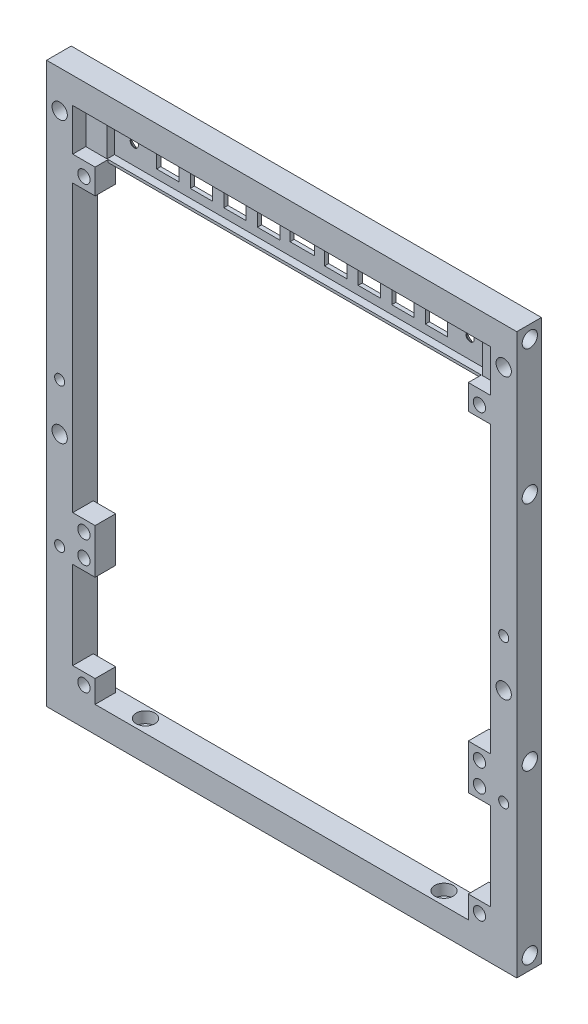
SolidWorks part; units mm, degrees
ref_plane "Front Plane" through (0, 0, 0) normal (0, 0, 1) x (1, 0, 0)
ref_plane "Top Plane" through (0, 0, 0) normal (0, 1, 0) x (1, 0, 0)
ref_plane "Right Plane" through (0, 0, 0) normal (1, 0, 0) x (0, 0, -1)
sketch "Sketch1" plane through (0, 0, 0) normal (0, 0, 1) x (1, 0, 0)
  line L1 (-63, -75) -> (63, -75)
  line L2 (-63, -75) -> (-63, 75)
  line L3 (-63, 75) -> (63, 75)
  line L4 (63, -75) -> (63, 75)
  line L5 (-63, -75) -> (63, 75) construction
  line L6 (-63, 75) -> (63, -75) construction
  line L7 (-56, -68) -> (56, -68)
  line L8 (-56, -68) -> (-56, 68)
  line L9 (-56, 68) -> (56, 68)
  line L10 (56, -68) -> (56, 68)
  line L11 (-56, -68) -> (56, 68) construction
  line L12 (-56, 68) -> (56, -68) construction
  point P0 (0, 0)
  point P6 (0, 0)
  dimension "D1" = 126
  dimension "D2" = 150
  dimension "D3" = 7
  dimension "D4" = 7
extrude "Boss-Extrude1" add sketch "Sketch1" along normal blind 7
sketch "Sketch2" plane through (-63, 0, 0) normal (-1, 0, 0) x (0, 0, 1)
  line L0 (3.5, 71.5) -> (3.5, -71.5) construction
  line L1 (7, 75) -> (0, 75) construction
  circle A0 centre (3.5, -71.5) radius 2.05
  circle A2 centre (3.5, 71.5) radius 2.05
  circle A3 centre (3.5, 35.5) radius 2.05
  circle A4 centre (3.5, -26.5) radius 2.05
  point P2 (3.5, 0)
  point P7 (3.5, 75)
  dimension "D2" = 4.1
  dimension "D3" = 36
  dimension "D4" = 45
  dimension "D1" = 3.5
extrude "Cut-Extrude1" cut sketch "Sketch2" against normal blind 6
mirror "Mirror1" about plane through (0, 0, 0) normal (1, 0, 0) of "Cut-Extrude1"
sketch "Sketch3" plane through (0, -68, 0) normal (0, 1, 0) x (1, 0, 0)
  line L0 (0, 0) -> (0, -7) construction
  line L1 (-56, 0) -> (56, 0) construction
  line L2 (-56, -7) -> (56, -7) construction
  line L3 (40, -3.5) -> (-40, -3.5) construction
  circle A0 centre (40, -3.5) radius 1.35
  circle A1 centre (-40, -3.5) radius 1.35
  point P9 (0, -3.5)
  dimension "D1" = 2.7
  dimension "D2" = 80
extrude "Cut-Extrude2" cut sketch "Sketch3" against normal through all
sketch "Sketch4" plane through (0, -68, 0) normal (0, 1, 0) x (1, 0, 0)
  circle A0 centre (40, -3.5) radius 2.5
  circle A1 centre (-40, -3.5) radius 2.5
  dimension "D1" = 5
extrude "Cut-Extrude3" cut sketch "Sketch4" against normal blind 3
sketch "Sketch5" plane through (0, 0, 0) normal (0, 0, -1) x (-1, 0, 0)
  line L0 (-59.5, -75) -> (-59.5, 75) construction
  line L1 (63, -75) -> (-63, -75) construction
  line L2 (-63, 75) -> (63, 75) construction
  line L3 (-56, 0) -> (-63, 0) construction
  line L4 (-56, -68) -> (-56, 68) construction
  line L5 (-63, -75) -> (-63, 75) construction
  line L6 (0, 75) -> (0, -75) construction
  line L7 (56, -68) -> (-56, -68) construction
  circle A0 centre (-59.5, 2.6) radius 1.35
  circle A1 centre (59.5, 2.6) radius 1.35
  circle A2 centre (-59.5, -36) radius 1.35
  circle A3 centre (59.5, -36) radius 1.35
  point P12 (-59.5, 0)
  point P13 (-59.5, 0)
  dimension "D1" = 2.7
  dimension "D2" = 2.6
  dimension "D3" = 32
extrude "Cut-Extrude4" cut sketch "Sketch5" against normal through all
sketch "Sketch6" plane through (0, 0, 0) normal (0, 0, -1) x (-1, 0, 0)
  circle A0 centre (-59.5, 2.6) radius 2.5
  circle A1 centre (59.5, 2.6) radius 2.5
  circle A2 centre (-59.5, -36) radius 2.5
  circle A3 centre (59.5, -36) radius 2.5
  dimension "D1" = 5
extrude "Cut-Extrude5" cut sketch "Sketch6" against normal blind 3
sketch "Sketch7" plane through (0, 0, 0) normal (0, 0, -1) x (-1, 0, 0)
  line L0 (-56, 68) -> (-63, 68) construction
  line L1 (-63, -75) -> (-63, 75) construction
  line L2 (-59.5, 65) -> (-59.5, -10) construction
  line L3 (-63, 75) -> (63, 75) construction
  circle A0 centre (-59.5, 65) radius 2.05
  circle A1 centre (-59.5, -10) radius 2.05
  point P8 (-59.5, 68)
  dimension "D1" = 4.1
  dimension "D2" = 10
  dimension "D3" = 75
extrude "Cut-Extrude6" cut sketch "Sketch7" against normal through all
mirror "Mirror2" about plane through (0, 0, 0) normal (1, 0, 0) of "Cut-Extrude6"
sketch "Sketch8" plane through (0, 0, 3) normal (0, 0, -1) x (-1, 0, 0)
  line L2 (-60.85, 0.4958) -> (-60.85, 4.7042)
  line L4 (-58.15, 0.4958) -> (-58.15, 4.7042)
  line L5 (-60.85, 0.4958) -> (-58.15, 4.7042) construction
  line L6 (-60.85, 4.7042) -> (-58.15, 0.4958) construction
  line L8 (-60.85, -38.1042) -> (-60.85, -33.8958)
  line L10 (-58.15, -38.1042) -> (-58.15, -33.8958)
  line L11 (-60.85, -38.1042) -> (-58.15, -33.8958) construction
  line L12 (-60.85, -33.8958) -> (-58.15, -38.1042) construction
  circle A0 centre (-59.5, 2.6) radius 2.5 construction
  circle A1 centre (-59.5, -36) radius 2.5 construction
  circle A2 centre (-59.5, -36) radius 2.5 construction
  arc A3 (-58.15, 4.7042) -> (-60.85, 4.7042) centre (-59.5, 2.6) ccw
  arc A4 (-58.15, -33.8958) -> (-60.85, -33.8958) centre (-59.5, -36) ccw
  circle A5 centre (-59.5, 2.6) radius 1.35 construction
  circle A6 centre (-59.5, -36) radius 1.35 construction
  arc A7 (-60.85, -38.1042) -> (-58.15, -38.1042) centre (-59.5, -36) ccw
  arc A8 (-60.85, 0.4958) -> (-58.15, 0.4958) centre (-59.5, 2.6) ccw
  point P0 (-59.5, 2.6)
  point P8 (-59.5, -36)
extrude "Cut-Extrude7" cut sketch "Sketch8" against normal blind 0.2
sketch "Sketch9" plane through (0, 0, 3.2) normal (0, 0, -1) x (-1, 0, 0)
  line L0 (-58.15, 2.6) -> (-58.15, 4.7042) construction
  line L1 (-60.85, 1.25) -> (-58.15, 1.25)
  line L2 (-60.85, 1.25) -> (-60.85, 3.95)
  line L3 (-60.85, 3.95) -> (-58.15, 3.95)
  line L4 (-58.15, 1.25) -> (-58.15, 3.95)
  line L5 (-60.85, 1.25) -> (-58.15, 3.95) construction
  line L6 (-60.85, 3.95) -> (-58.15, 1.25) construction
  line L7 (-58.15, -38.1042) -> (-58.15, -33.8958) construction
  line L8 (-60.85, -37.35) -> (-58.15, -37.35)
  line L9 (-60.85, -37.35) -> (-60.85, -34.65)
  line L10 (-60.85, -34.65) -> (-58.15, -34.65)
  line L11 (-58.15, -37.35) -> (-58.15, -34.65)
  line L12 (-60.85, -37.35) -> (-58.15, -34.65) construction
  line L13 (-60.85, -34.65) -> (-58.15, -37.35) construction
  arc A0 (-58.15, 2.6) -> (-60.85, 2.6) centre (-59.5, 2.6) ccw construction
  point P0 (-59.5, 2.6)
  point P8 (-59.5, -36)
extrude "Cut-Extrude8" cut sketch "Sketch9" against normal blind 0.2
mirror "Mirror3" about plane through (0, 0, 0) normal (1, 0, 0) of "Cut-Extrude8", "Cut-Extrude7"
sketch "Sketch10" plane through (0, 0, 7) normal (0, 0, 1) x (1, 0, 0)
  line L0 (56, -68) -> (56, 68) construction
  line L1 (56, -68) -> (50, -68)
  line L2 (56, -68) -> (56, -62)
  line L3 (56, -62) -> (50, -62)
  line L4 (50, -68) -> (50, -62)
  line L5 (56, -38.5) -> (50, -38.5)
  line L6 (56, -38.5) -> (56, -32.5)
  line L7 (56, -32.5) -> (50, -32.5)
  line L8 (50, -38.5) -> (50, -32.5)
  line L9 (-56, -68) -> (56, -68) construction
  dimension "D1" = 6
  dimension "D2" = 35.5
extrude "Boss-Extrude2" add sketch "Sketch10" against normal offset from surface (5.5 mm away) 1.5 up to face at (-57.45, -10, 0)
sketch "Sketch11" plane through (0, 0, 1.5) normal (0, 0, -1) x (-1, 0, 0)
  line L0 (-56, -38.5) -> (-50, -32.5) construction
  line L2 (-56, -68) -> (-50, -62) construction
  circle A0 centre (-53, -35.5) radius 1.65
  circle A1 centre (-53, -65) radius 1.65
  dimension "D1" = 3.3
extrude "Cut-Extrude9" cut sketch "Sketch11" against normal through all
mirror "Mirror4" about plane through (0, 0, 0) normal (1, 0, 0) of "Cut-Extrude9", "Boss-Extrude2"
sketch "Sketch12" plane through (0, 0, 0) normal (0, 0, -1) x (-1, 0, 0)
  line L0 (56, 68) -> (56, -68) construction
  line L1 (-56, 68) -> (56, 68)
  line L2 (-56, 68) -> (-56, 56)
  line L3 (-56, 56) -> (56, 56)
  line L4 (56, 68) -> (56, 56)
  dimension "D1" = 12
extrude "Boss-Extrude3" add sketch "Sketch12" against normal blind 1.5
sketch "Sketch13" plane through (0, 0, 1.5) normal (0, 0, 1) x (1, 0, 0)
  line L0 (-56, 68) -> (56, 56) construction
  line L2 (-50.3, 56.7) -> (50.3, 56.7)
  line L3 (-50.3, 56.7) -> (-50.3, 67.3)
  line L4 (-50.3, 67.3) -> (50.3, 67.3)
  line L5 (50.3, 56.7) -> (50.3, 67.3)
  line L6 (-50.3, 56.7) -> (50.3, 67.3) construction
  line L7 (-50.3, 67.3) -> (50.3, 56.7) construction
  line L8 (-56, 56) -> (56, 56)
  line L9 (-56, 56) -> (-56, 68)
  line L10 (-56, 68) -> (56, 68)
  line L11 (56, 56) -> (56, 68)
  line L12 (-56, 56) -> (56, 68) construction
  line L13 (-56, 68) -> (56, 56) construction
  point P4 (0, 62)
  point P9 (0, 62)
  dimension "D1" = 100.6
  dimension "D2" = 10.6
extrude "Boss-Extrude4" add sketch "Sketch13" along normal blind 2
sketch "Sketch14" plane through (0, 0, 1.5) normal (0, 0, 1) x (1, 0, 0)
  line L0 (0, 67.3) -> (0, 56.7) construction
  line L1 (50.3, 67.3) -> (-50.3, 67.3) construction
  line L2 (-50.3, 56.7) -> (50.3, 56.7) construction
  line L3 (-50.3, 62) -> (50.3, 62) construction
  line L4 (50.3, 56.7) -> (50.3, 67.3) construction
  line L5 (-33, 65) -> (-39, 65)
  line L6 (-3.25, 60) -> (3.25, 60)
  line L7 (-3.25, 60) -> (-3.25, 64)
  line L8 (-3.25, 64) -> (3.25, 64)
  line L9 (3.25, 60) -> (3.25, 64)
  line L10 (-3.25, 60) -> (3.25, 64) construction
  line L11 (-3.25, 64) -> (3.25, 60) construction
  line L12 (6, 59) -> (12, 59)
  line L13 (6, 59) -> (6, 65)
  line L14 (6, 65) -> (12, 65)
  line L15 (12, 59) -> (12, 65)
  line L16 (6, 59) -> (12, 65) construction
  line L17 (6, 65) -> (12, 59) construction
  line L18 (15, 59) -> (21, 59)
  line L19 (15, 59) -> (15, 65)
  line L20 (15, 65) -> (21, 65)
  line L21 (21, 59) -> (21, 65)
  line L22 (15, 59) -> (21, 65) construction
  line L23 (15, 65) -> (21, 59) construction
  line L24 (24, 59) -> (30, 59)
  line L25 (24, 59) -> (24, 65)
  line L26 (24, 65) -> (30, 65)
  line L27 (30, 59) -> (30, 65)
  line L28 (24, 59) -> (30, 65) construction
  line L29 (24, 65) -> (30, 59) construction
  line L30 (33, 59) -> (39, 59)
  line L31 (33, 59) -> (33, 65)
  line L32 (33, 65) -> (39, 65)
  line L33 (39, 59) -> (39, 65)
  line L34 (33, 59) -> (39, 65) construction
  line L35 (33, 65) -> (39, 59) construction
  line L36 (-39, 59) -> (-39, 65)
  line L37 (-33, 59) -> (-39, 59)
  line L38 (-33, 59) -> (-33, 65)
  line L39 (-24, 65) -> (-30, 65)
  line L40 (-30, 59) -> (-30, 65)
  line L41 (-24, 59) -> (-30, 59)
  line L42 (-24, 59) -> (-24, 65)
  line L43 (-15, 65) -> (-21, 65)
  line L44 (-21, 59) -> (-21, 65)
  line L45 (-15, 59) -> (-21, 59)
  line L46 (-15, 59) -> (-15, 65)
  line L47 (-6, 65) -> (-12, 65)
  line L48 (-12, 59) -> (-12, 65)
  line L49 (-6, 59) -> (-12, 59)
  line L50 (-6, 59) -> (-6, 65)
  circle A0 centre (-45, 62) radius 1.3 construction
  circle A1 centre (45, 62) radius 1.3 construction
  point P6 (0, 62)
  point P11 (0, 62)
  point P16 (9, 62)
  point P21 (18, 62)
  point P26 (27, 62)
  point P31 (36, 62)
  dimension "D10" = 2.6
  dimension "D9" = 45
  dimension "D1" = 6.5
  dimension "D2" = 4
  dimension "D3" = 6
  dimension "D4" = 9
  dimension "D5" = 9
  dimension "D6" = 9
  dimension "D7" = 9
  dimension "D8" = 45
extrude "Cut-Extrude10" cut sketch "Sketch14" against normal through all
sketch "Sketch15" plane through (0, 0, 1.5) normal (0, 0, 1) x (1, 0, 0)
  circle A0 centre (-45, 62) radius 1
  circle A1 centre (45, 62) radius 1
  dimension "D1" = 2
extrude "Boss-Extrude5" add sketch "Sketch15" along normal up to surface (2 mm away) up to face at (0, 62, 3.5)
chamfer "Chamfer1" distance 0.4 angle 45 4 edges at (-56, -6, 0) (56, -6, 0) (0, -68, 0) (0, 56, 0)
chamfer "Chamfer2" distance 0.4 angle 45 4 edges at (0, 75, 0) (-63, 0, 0) (0, -75, 0) (63, 0, 0)
chamfer "Chamfer3" distance 0.4 angle 45 36 edges at (-36, 59, 0) (-39, 62, 0) (-36, 65, 0) (-33, 62, 0) (-27, 59, 0) (-30, 62, 0) (-27, 65, 0) (-24, 62, 0) (-18, 59, 0) (-21, 62, 0) (-18, 65, 0) (-15, 62, 0) (-9, 59, 0) (-12, 62, 0) (-9, 65, 0) (-6, 62, 0) (0, 60, 0) (-3.25, 62, 0) (0, 64, 0) (3.25, 62, 0) (9, 59, 0) (6, 62, 0) (9, 65, 0) (12, 62, 0) (18, 59, 0) (15, 62, 0) (18, 65, 0) (21, 62, 0) (36, 59, 0) (33, 62, 0) (36, 65, 0) (39, 62, 0) (27, 59, 0) (24, 62, 0) (27, 65, 0) (30, 62, 0)
sketch "Sketch16" plane through (0, 0, 7) normal (0, 0, 1) x (1, 0, 0)
  line L0 (-50, 56) -> (-50, 56.7)
  line L1 (-56, -32.5) -> (-50, -32.5)
  line L2 (-56, -32.5) -> (-56, -26.5)
  line L3 (-56, -26.5) -> (-50, -26.5)
  line L4 (-50, -32.5) -> (-50, -26.5)
  line L5 (56, -32.5) -> (50, -32.5)
  line L6 (56, -32.5) -> (56, -26.5)
  line L7 (56, -26.5) -> (50, -26.5)
  line L8 (50, -32.5) -> (50, -26.5)
  line L9 (56, 56) -> (50, 56) construction
  line L10 (56, 56) -> (56, 50)
  line L11 (56, 50) -> (50, 50)
  line L12 (50, 56) -> (50, 50)
  line L13 (-56, 56) -> (-50, 56) construction
  line L14 (-56, 56) -> (-56, 50)
  line L15 (-56, 50) -> (-50, 50)
  line L16 (-50, 56) -> (-50, 50)
  line L17 (-50.3, 56.7) -> (50.3, 56.7) construction
  line L18 (-50, 56.7) -> (-56, 56.7)
  line L19 (-56, 68) -> (-56, 56) construction
  line L20 (-56, 56.7) -> (-56, 56)
  line L21 (50, 56) -> (50, 56.7)
  line L22 (50, 56.7) -> (56, 56.7)
  line L23 (56, 56) -> (56, 68) construction
  line L24 (56, 56.7) -> (56, 56)
  dimension "D1" = 6
extrude "Boss-Extrude7" add sketch "Sketch16" against normal offset from surface (5.5 mm away) 1.5 up to face at (-36, 62, 0)
sketch "Sketch17" plane through (0, 0, 1.5) normal (0, 0, -1) x (-1, 0, 0)
  line L0 (-50, 50) -> (50, -26.5) construction
  line L1 (-50, -26.5) -> (-50, -38.5) construction
  line L2 (-53, -29.5) -> (53, -29.5) construction
  line L3 (-53, -29.5) -> (-53, 53) construction
  line L4 (-53, 53) -> (53, 53) construction
  line L5 (53, -29.5) -> (53, 53) construction
  line L6 (-53, -29.5) -> (53, 53) construction
  line L7 (-53, 53) -> (53, -29.5) construction
  line L8 (50, -26.5) -> (56, -26.5) construction
  circle A0 centre (-53, -29.5) radius 1.65
  circle A1 centre (53, -29.5) radius 1.65
  circle A2 centre (53, 53) radius 1.65
  circle A3 centre (-53, 53) radius 1.65
  point P4 (0, 11.75)
  dimension "D3" = 3.3
  dimension "D1" = 3
  dimension "D2" = 3
extrude "Cut-Extrude11" cut sketch "Sketch17" against normal through all
sketch "Sketch18" plane through (0, 0, 1.5) normal (0, 0, 1) x (1, 0, 0)
  circle A0 centre (-45, 62) radius 1.1
  circle A1 centre (45, 62) radius 1.1
  dimension "D1" = 2.2
extrude "Cut-Extrude12" cut sketch "Sketch18" against normal through all both and the other way through all
chamfer "Chamfer4" distance 1.3 angle 45 2 edges at (-43.9, 62, 0) (46.1, 62, 0)
